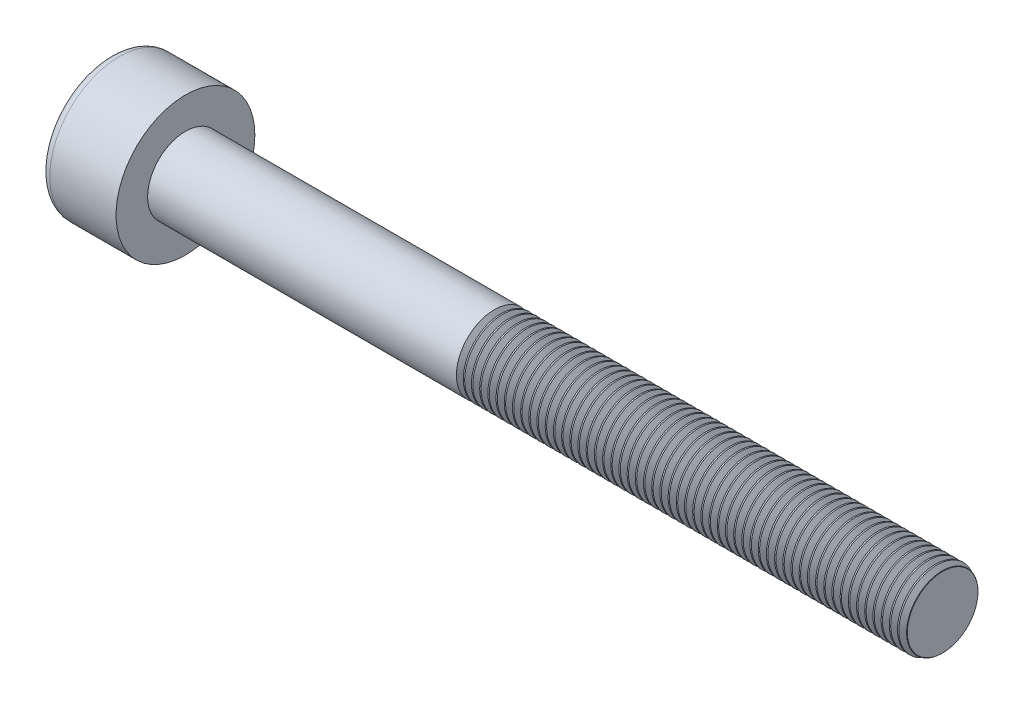
SolidWorks part; units mm, degrees
ref_plane "Front" through (0, 0, 0) normal (0, 0, 1) x (1, 0, 0)
ref_plane "Top" through (0, 0, 0) normal (0, 1, 0) x (1, 0, 0)
ref_plane "Right" through (0, 0, 0) normal (1, 0, 0) x (0, 0, -1)
sketch "Sketch1" plane through (0, 0, 0) normal (1, 0, 0) x (0, 0, -1)
  circle A0 centre (0, 0) radius 2.75
  dimension "dk" = 5.5
extrude "BaseHead" add sketch "Sketch1" along normal blind 3
sketch "Sketch2" plane through (3, 0, 0) normal (1, 0, 0) x (0, 0, -1)
  circle A0 centre (0, 0) radius 1.5
  dimension "d" = 3
extrude "BaseBody" add sketch "Sketch2" along normal blind 30
cosmetic thread "ThreadCosmetic1" [suppressed] parameters "b"=18, "D2"=2.459
sketch "Sketch3" plane through (0, 0, 0) normal (1, 0, 0) x (0, 0, -1)
  line L1 (1.4434, 0) -> (0.7217, 1.25)
  line L2 (0.7217, 1.25) -> (-0.7217, 1.25)
  line L3 (-0.7217, 1.25) -> (-1.4434, 0)
  line L4 (-1.4434, 0) -> (-0.7217, -1.25)
  line L5 (-0.7217, -1.25) -> (0.7217, -1.25)
  line L6 (0.7217, -1.25) -> (1.4434, 0)
  circle A0 centre (0, 0) radius 1.25 construction
  dimension "s" = 2.5
  dimension "e" = 2.8868
extrude "HexagonSocket" cut sketch "Sketch3" along normal blind 1.3
sketch "Sketch4" plane through (-4.1961, 0.75, 0) normal (0, 0, 1) x (-1, 0, 0)
  line L0 (-5.4961, 2) -> (-6.2178, 0.75)
  line L2 (-6.2178, 0.75) -> (-5.4961, 0.75)
  line L3 (-5.4961, 0.75) -> (-5.4961, 2)
  line L4 (-5.0351, 0.75) -> (0.839, 0.75) construction
  line L5 (-37.1961, 0.75) -> (-7.1961, 0.75) construction
  line L6 (-7.1961, 0.75) -> (-4.1961, 0.75) construction
  dimension "m" = 60
revolve "Cut-Revolve1" cut sketch "Sketch4" angle 360 about L4
fillet "HeadFillet" [suppressed] radius 0.1
fillet "TopFillet" radius 0.375 1 edges at (0, 0, -2.75)
chamfer "Chamfer1" distance 0.1 angle 45 1 edges at (33, 0, -1.5)
sketch "Sketch5" plane through (0, 0, 0) normal (0, 0, 1) x (1, 0, 0)
  line L0 (32.9, 1.2657) -> (33.0353, 1.5)
  line L1 (33.0353, 1.5) -> (33.0353, 1.7705)
  line L2 (33.0353, 1.7705) -> (32.7648, 1.7705)
  line L3 (32.7648, 1.7705) -> (32.7648, 1.5)
  line L4 (32.7648, 1.5) -> (32.9, 1.2657)
  line L5 (0, 0) -> (7.8886, 0) construction
  line L6 (32.9, -1.5) -> (32.9, 1.5) construction
  dimension "D1" = 3
  dimension "D2" = 0.2705
revolve "Cut-Revolve10" cut sketch "Sketch5" angle 360 about L5
pattern_linear "LPattern10" count 55 spacing 0.3246 along (-1, 0, 0) of "Cut-Revolve10"
equation "\"r1@TopFillet\" = \"d@Sketch2\" / 8"
equation "\"D1@Chamfer1\" = \"r@HeadFillet\""
equation "\"D1@Sketch5\" = \"d@Sketch2\""
equation "\"D2@Sketch5\" =  ( \"d@Sketch2\" - \"D2@ThreadCosmetic1\" )  / 2"
equation "\"D3@LPattern10\" = \"D2@Sketch5\" * 1.2"
equation "\"D1@LPattern10\" = \"b@ThreadCosmetic1\" / \"D3@LPattern10\""
